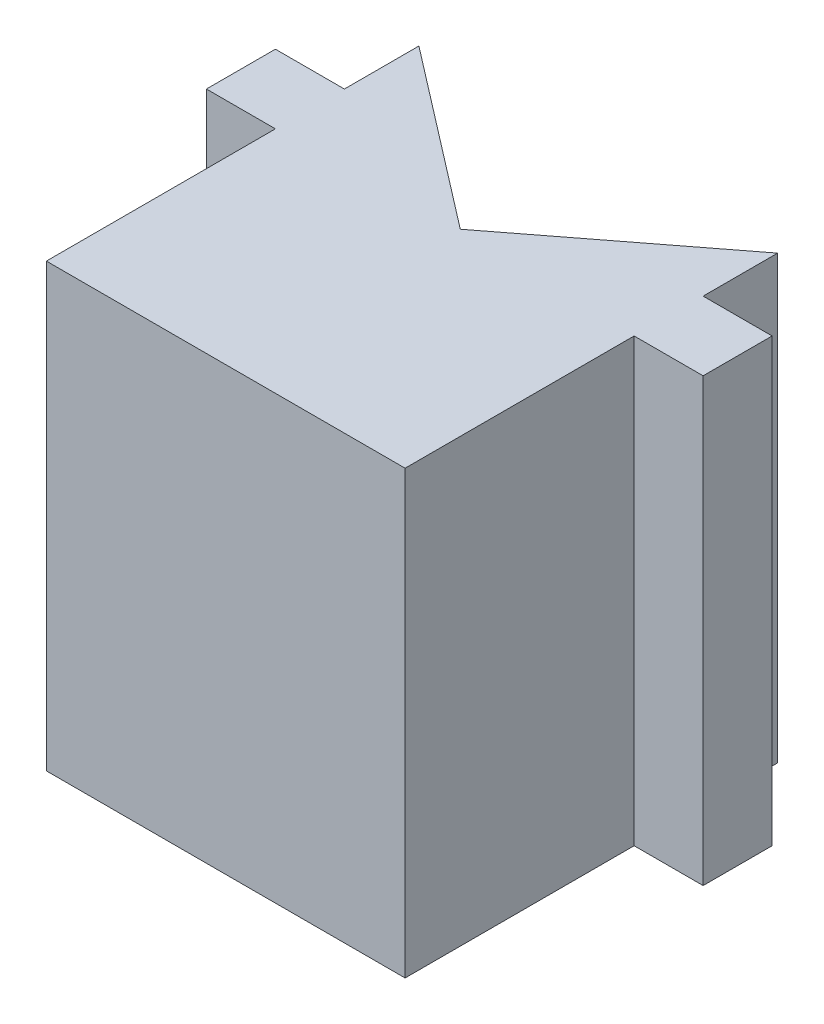
SolidWorks part; units mm, degrees
ref_plane "Front Plane" through (0, 0, 0) normal (0, 0, 1) x (1, 0, 0)
ref_plane "Top Plane" through (0, 0, 0) normal (0, 1, 0) x (1, 0, 0)
ref_plane "Right Plane" through (0, 0, 0) normal (1, 0, 0) x (0, 0, -1)
sketch "Sketch2" plane through (0, 0, 0) normal (0, 1, 0) x (1, 0, 0)
  line L0 (0, 0) -> (0, 21.082)
  line L1 (0, 0) -> (-33.02, 0)
  line L2 (-33.02, 0) -> (-33.02, 21.082)
  line L3 (0, 21.082) -> (6.35, 21.082)
  line L4 (-33.02, 21.082) -> (-39.37, 21.082)
  line L5 (6.35, 21.082) -> (6.35, 27.432)
  line L6 (6.35, 27.432) -> (0, 27.432)
  line L7 (0, 27.432) -> (0, 21.082)
  line L8 (-33.02, 21.082) -> (-33.02, 27.432)
  line L9 (-33.02, 27.432) -> (-39.37, 27.432)
  line L10 (-39.37, 27.432) -> (-39.37, 21.082)
  line L11 (-16.51, 0) -> (-16.51, 21.59) construction
  line L12 (0, 27.432) -> (0, 34.29)
  line L13 (-33.02, 27.432) -> (-33.02, 34.29)
  line L14 (0, 34.29) -> (-16.51, 21.59)
  line L15 (-16.51, 21.59) -> (-33.02, 34.29)
  line L16 (-16.51, 0) -> (-16.51, 12.954) construction
  dimension "D1" = 33.02
  dimension "D2" = 34.29
  dimension "D3" = 6.35
  dimension "D4" = 6.35
  dimension "D5" = 90
  dimension "D6" = 90
  dimension "D7" = 12.7
  dimension "D8" = 6.35
  dimension "D9" = 6.35
  dimension "D10" = 21.082
  dimension "D11" = 21.082
  dimension "D12" = 20.8295
  dimension "D13" = 12.954
extrude "Boss-Extrude1" add sketch "Sketch2" along normal blind 40.64
sketch "Sketch5" plane through (0, 0, 0) normal (0, -1, 0) x (1, 0, 0)
  line L0 (0, -34.29) -> (-33.02, -34.29)
  line L1 (0, -34.29) -> (-16.51, -21.59)
  line L2 (-16.51, -21.59) -> (-33.02, -34.29)
extrude "Boss-Extrude2" add sketch "Sketch5" against normal blind 2.54
